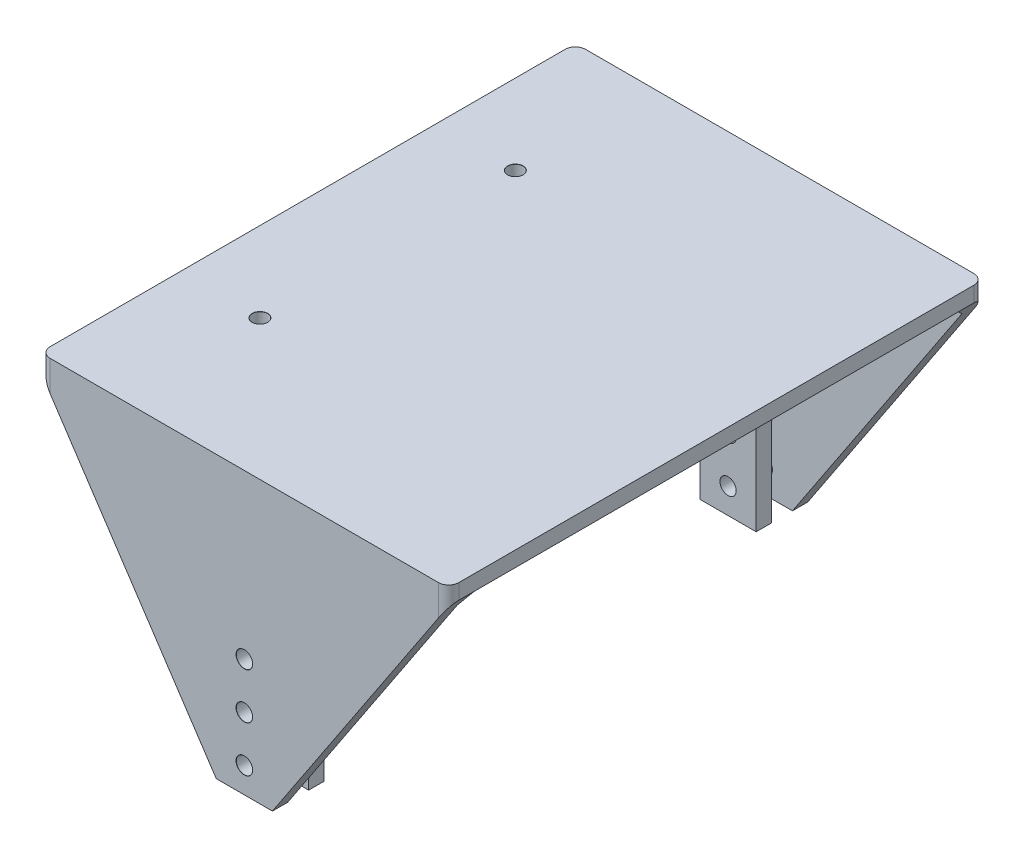
SolidWorks part; units mm, degrees
material "ABS"
ref_plane "Front Plane" through (0, 0, 0) normal (0, 0, 1) x (1, 0, 0)
ref_plane "Top Plane" through (0, 0, 0) normal (0, 1, 0) x (1, 0, 0)
ref_plane "Right Plane" through (0, 0, 0) normal (1, 0, 0) x (0, 0, -1)
sketch "Sketch1" plane through (0, 0, 0) normal (0, 1, 0) x (1, 0, 0)
  line L0 (-19.4927, 0) -> (33.7086, 0) construction
  line L1 (-40, -49.4) -> (40, -49.4)
  line L2 (-40, -49.4) -> (-40, 49.4)
  line L3 (-40, 49.4) -> (40, 49.4)
  line L4 (40, -49.4) -> (40, 49.4)
  line L5 (0, 23.6315) -> (0, -27.4954) construction
  point P0 (0, 0)
  dimension "D1" = 80
  dimension "D2" = 98.8
extrude "Boss-Extrude1" add sketch "Sketch1" along normal blind 3
sketch "Sketch3" plane through (0, 0, 49.4) normal (0, 0, 1) x (1, 0, 0)
  line L0 (-40, 0) -> (-40, 3)
  line L1 (-40, 3) -> (40, 3)
  line L2 (40, 3) -> (40, 0) construction
  line L3 (-40, 3) -> (40, 3) construction
  line L4 (40, 3) -> (40, 0)
  line L5 (40, 0) -> (5.5, -52)
  line L6 (5.5, -52) -> (-5.5, -52)
  line L7 (-5.5, -52) -> (-40, 0)
  line L8 (0, 10.1365) -> (0, -10.768) construction
  dimension "D1" = 11
  dimension "D2" = 55
extrude "Boss-Extrude2" add sketch "Sketch3" along normal blind 3
mirror "Mirror1" about plane through (0, 0, 0) normal (0, 0, 1) of "Boss-Extrude2"
chamfer "Chamfer2" distance 2 angle 45 2 edges at (0, 0, -49.4) (0, 0, 49.4)
fillet "Fillet1" radius 2 4 edges at (-40, 1.5, 52.4) (-40, 1.5, -52.4) (40, 1.5, -52.4) (40, 1.5, 52.4)
sketch "Sketch4" plane through (0, 0, 49.4) normal (0, 0, -1) x (-1, 0, 0)
  line L0 (5.5, -52) -> (-5.5, -52) construction
  line L2 (-5.5, -19.9) -> (5.5, -19.9)
  line L3 (-5.5, -19.9) -> (-5.5, -22.9)
  line L4 (-5.5, -22.9) -> (5.5, -22.9)
  line L5 (5.5, -19.9) -> (5.5, -22.9)
  dimension "D1" = 29.1
  dimension "D2" = 3
extrude "Boss-Extrude3" add sketch "Sketch4" along normal blind 4.1
sketch "Sketch6" plane through (0, 0, 45.3) normal (0, 0, -1) x (-1, 0, 0)
  line L0 (5.5, -19.9) -> (-5.5, -19.9) construction
  line L1 (-5.5, -52) -> (5.5, -52)
  line L2 (-5.5, -52) -> (-5.5, -19.9)
  line L3 (-5.5, -19.9) -> (5.5, -19.9)
  line L4 (5.5, -52) -> (5.5, -19.9)
extrude "Boss-Extrude4" add sketch "Sketch6" along normal blind 3
mirror "Mirror4" about plane through (0, 0, 0) normal (0, 0, 1) of "Boss-Extrude4", "Boss-Extrude3"
chamfer "Chamfer3" distance 2 angle 45 2 edges at (0, -19.9, 49.4) (0, -19.9, -49.4)
hole_wizard "Ø3.0mm Dowel Hole1" positions "Sketch7" profile "Sketch8" hole size "Ø3.0" standard "ANSI Metric" end condition through all
sketch "Sketch7" plane through (0, 0, 52.4) normal (0, 0, 1) x (1, 0, 0)
  line L0 (-5.5, -52) -> (5.5, -52) construction
  point P0 (0, -47)
  point P2 (0, -38)
  point P4 (0, -29)
  dimension "D1" = 9
  dimension "D2" = 9
  dimension "D3" = 5
sketch "Sketch8" plane through (0, -47, 52.4) normal (1, 0, 0) x (0, -1, 0)
  line L0 (0, 0) -> (0, 104.8)
  line L1 (0, 104.8) -> (1.6, 104.8)
  line L2 (1.6, 104.8) -> (1.6, 0.025)
  line L3 (1.6, 0.025) -> (1.625, 0)
  line L5 (1.625, 0) -> (0, 0)
  line L6 (-1.6, 0.025) -> (-1.625, 0) construction
  line L11 (0, -6.35) -> (0, 107.95) construction
  dimension "Thru Hole Dia." = 3.2
  dimension "Thru Hole Depth" = 104.8
  dimension "Near C'Sink Dia." = 3.25
  dimension "Near C'Sink Angle" = 90
hole_wizard "Ø3.0mm Dowel Hole2" positions "Sketch9" profile "Sketch10" hole size "Ø3.0" standard "ANSI Metric"
sketch "Sketch9" plane through (0, 3, 0) normal (0, 1, 0) x (1, 0, 0)
  line L0 (-16.85, 25) -> (-31.85, 25) construction
  line L1 (-31.85, -25) -> (-16.85, -25) construction
  point P0 (-24.35, 25)
  point P4 (-24.35, -25)
sketch "Sketch10" plane through (-24.35, 3, -25) normal (1, 0, 0) x (0, 0, 1)
  line L0 (0, 0) -> (0, 20.9013)
  line L1 (0, 20.9013) -> (1.5, 20)
  line L2 (1.5, 20) -> (1.5, 0.025)
  line L3 (1.5, 0.025) -> (1.525, 0)
  line L5 (1.525, 0) -> (0, 0)
  line L6 (-1.5, 0.025) -> (-1.525, 0) construction
  line L10 (0, 20.9013) -> (-1.5, 20) construction
  line L11 (0, -6.35) -> (0, 107.95) construction
  dimension "Hole Dia." = 3
  dimension "Hole Depth" = 20
  dimension "Near C'Sink Dia." = 3.05
  dimension "Near C'Sink Angle" = 90
  dimension "Drill Angle" = 118
